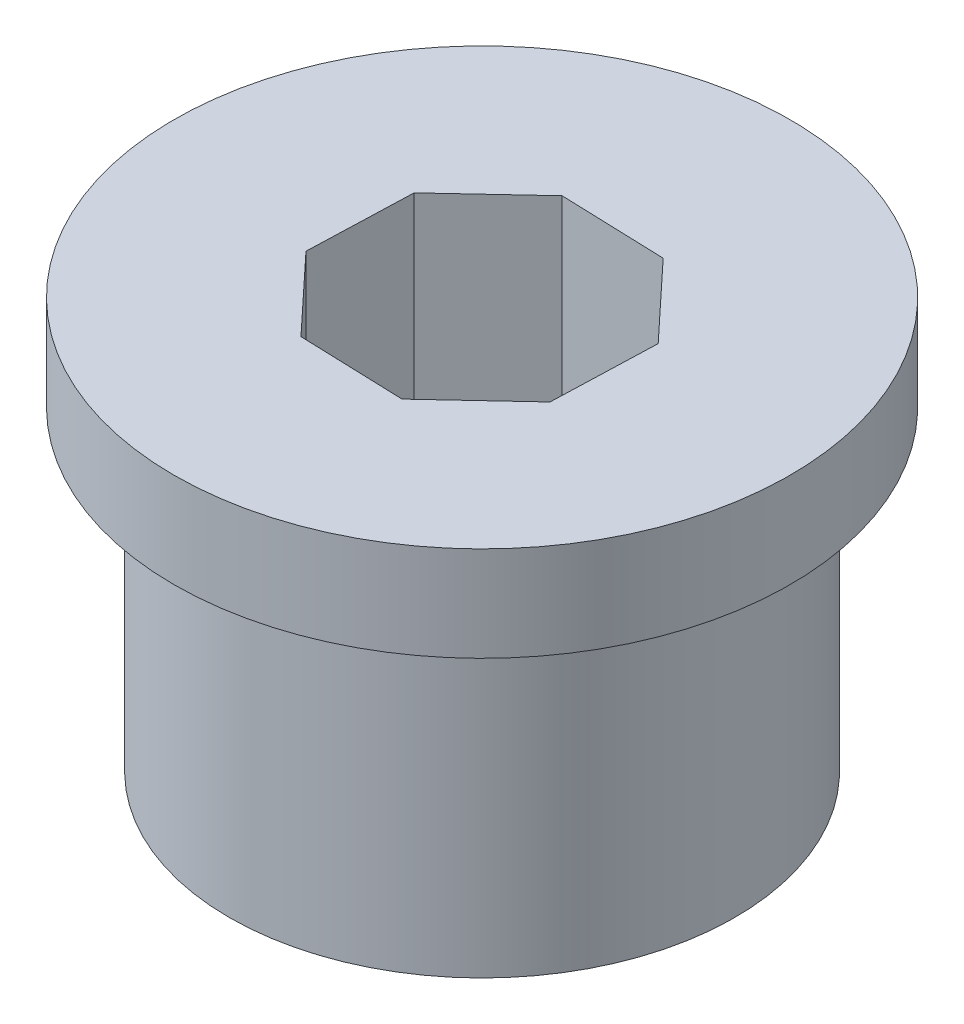
SolidWorks part; units mm, degrees
material "ABS"
ref_plane "Front Plane" through (0, 0, 0) normal (0, 0, 1) x (1, 0, 0)
ref_plane "Top Plane" through (0, 0, 0) normal (0, 1, 0) x (1, 0, 0)
ref_plane "Right Plane" through (0, 0, 0) normal (1, 0, 0) x (0, 0, -1)
sketch "Sketch1" plane through (0, 0, 0) normal (0, 1, 0) x (1, 0, 0)
  circle A0 centre (0, 0) radius 8
  dimension "D1" = 16
extrude "Boss-Extrude1" add sketch "Sketch1" along normal blind 10
sketch "Sketch2" plane through (0, 10, 0) normal (0, 1, 0) x (1, 0, 0)
  circle A0 centre (0, 0) radius 9.75
  dimension "D1" = 19.5
extrude "Boss-Extrude2" add sketch "Sketch2" along normal blind 3
sketch "Sketch3" plane through (0, 13, 0) normal (0, 1, 0) x (1, 0, 0)
  line L1 (3.9416, -1.7913) -> (4.0538, 1.5205)
  line L2 (4.0538, 1.5205) -> (1.7913, 3.9416)
  line L3 (1.7913, 3.9416) -> (-1.5205, 4.0538)
  line L4 (-1.5205, 4.0538) -> (-3.9416, 1.7913)
  line L5 (-3.9416, 1.7913) -> (-4.0538, -1.5205)
  line L6 (-4.0538, -1.5205) -> (-1.7913, -3.9416)
  line L7 (-1.7913, -3.9416) -> (1.5205, -4.0538)
  line L8 (1.5205, -4.0538) -> (3.9416, -1.7913)
  circle A0 centre (0, 0) radius 4 construction
  dimension "D1" = 8
extrude "Cut-Extrude1" cut sketch "Sketch3" against normal through all
